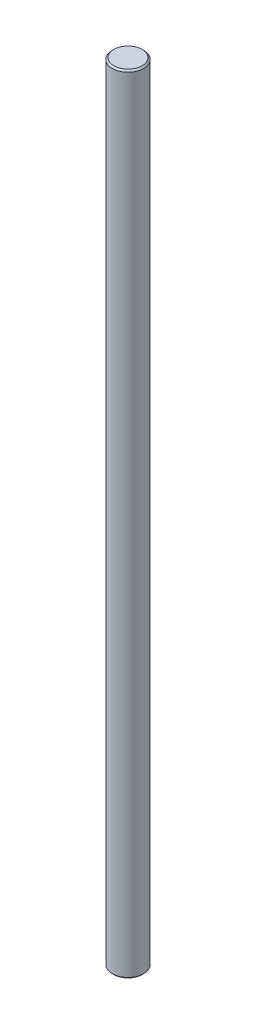
SolidWorks part; units mm, degrees
material "Plain Carbon Steel"
ref_plane "Front Plane" through (0, 0, 0) normal (0, 0, 1) x (1, 0, 0)
ref_plane "Top Plane" through (0, 0, 0) normal (0, 1, 0) x (1, 0, 0)
ref_plane "Right Plane" through (0, 0, 0) normal (1, 0, 0) x (0, 0, -1)
sketch "Sketch1" plane through (0, 0, 0) normal (0, 1, 0) x (1, 0, 0)
  circle A0 centre (0, 0) radius 10
  dimension "D1" = 20
extrude "Boss-Extrude1" add sketch "Sketch1" along normal blind 500
chamfer "Chamfer1" distance 1 angle 45 2 edges at (0, 500, 10) (0, 0, 10)
